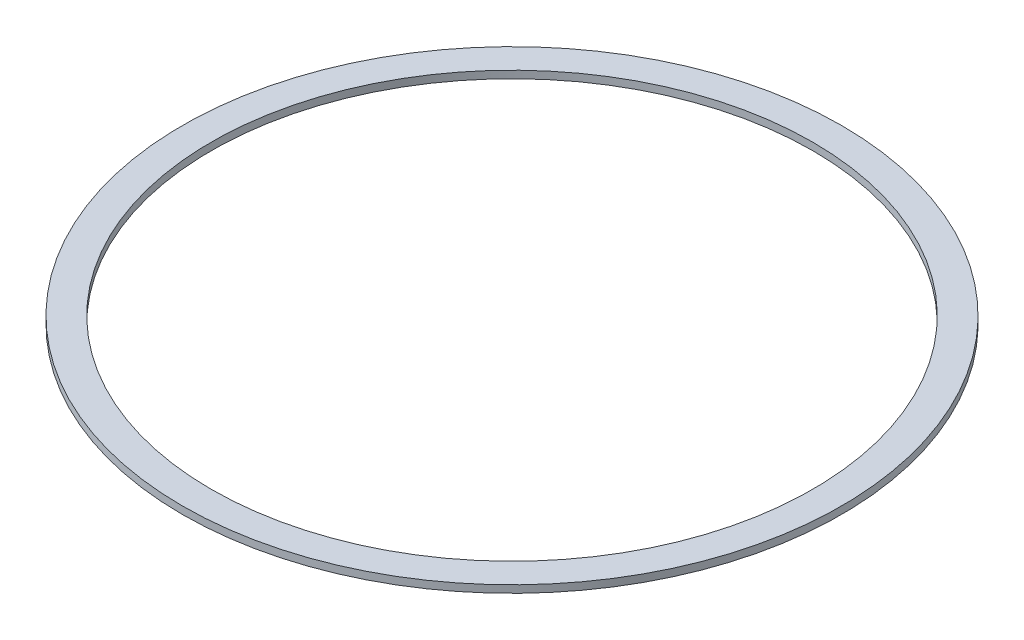
SolidWorks part; units mm, degrees
ref_plane "Front Plane" through (0, 0, 0) normal (0, 0, 1) x (1, 0, 0)
ref_plane "Top Plane" through (0, 0, 0) normal (0, 1, 0) x (1, 0, 0)
ref_plane "Right Plane" through (0, 0, 0) normal (1, 0, 0) x (0, 0, -1)
sketch "Sketch1" plane through (0, 0, 0) normal (0, 1, 0) x (1, 0, 0)
  circle A1 centre (0, 0) radius 73
  circle A2 centre (0, 0) radius 80
  dimension "D1" = 146
  dimension "D2" = 160
extrude "Boss-Extrude1" add sketch "Sketch1" along normal blind 1.8
